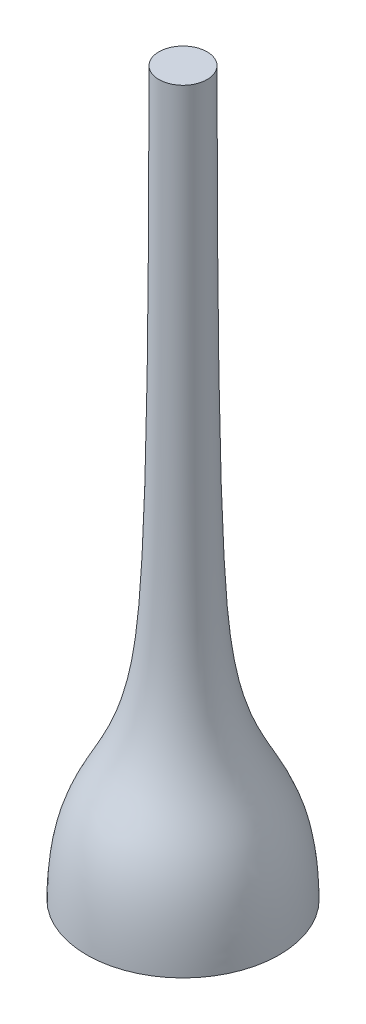
SolidWorks part; units mm, degrees
ref_plane "Front Plane" through (0, 0, 0) normal (0, 0, 1) x (1, 0, 0)
ref_plane "Top Plane" through (0, 0, 0) normal (0, 1, 0) x (1, 0, 0)
ref_plane "Right Plane" through (0, 0, 0) normal (1, 0, 0) x (0, 0, -1)
sketch "Sketch1" plane through (0, 0, 0) normal (0, 0, 1) x (1, 0, 0)
  line L0 (0, 15) -> (0, 0)
  line L1 (0, 0) -> (2, 0)
  line L2 (0, 15) -> (0.5, 15)
  spline S0 degree 3 poles (0.5, 15) (0.5017, 9.6608) (0.5714, 5.9949) (0.942, 2.0336) (1.97, 2.3515) (2, 0) knots 0 0 0 0 0.230232 0.330232 1 1 1 1
  point P6 (0, 0)
  point P7 (0, 0)
  point P8 (0.9915, 5.404)
  point P9 (0.4053, 5.4204)
  point P10 (0.5707, 5.3079)
  point P11 (0.6503, 5.2651)
  dimension "D1" = 15
  dimension "D2" = 2
  dimension "D3" = 0.5
revolve "Revolve8" add sketch "Sketch1" angle 360 about L0
